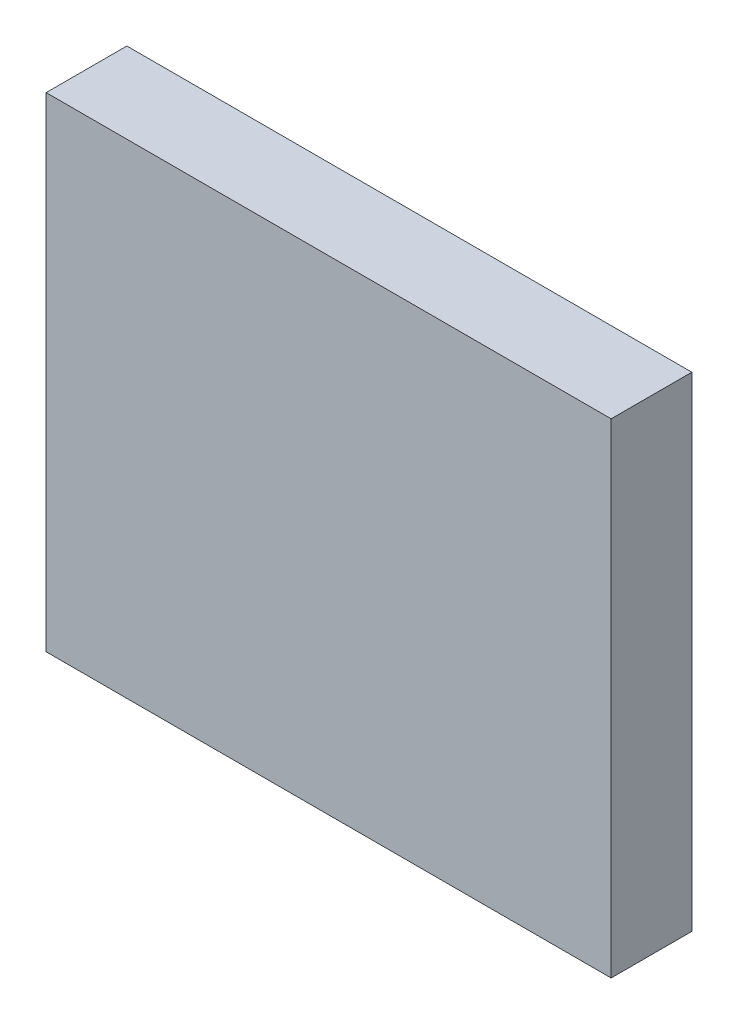
SolidWorks part; units mm, degrees
ref_plane "Front Plane" through (0, 0, 0) normal (0, 0, 1) x (1, 0, 0)
ref_plane "Top Plane" through (0, 0, 0) normal (0, 1, 0) x (1, 0, 0)
ref_plane "Right Plane" through (0, 0, 0) normal (1, 0, 0) x (0, 0, -1)
sketch "Sketch1" plane through (0, 0, 0) normal (0, 0, 1) x (1, 0, 0)
  line L1 (-14, -12) -> (14, -12)
  line L2 (-14, -12) -> (-14, 12)
  line L3 (-14, 12) -> (14, 12)
  line L4 (14, -12) -> (14, 12)
  line L5 (-14, -12) -> (14, 12) construction
  line L6 (-14, 12) -> (14, -12) construction
extrude "Boss-Extrude1" add sketch "Sketch1" along normal blind 4
